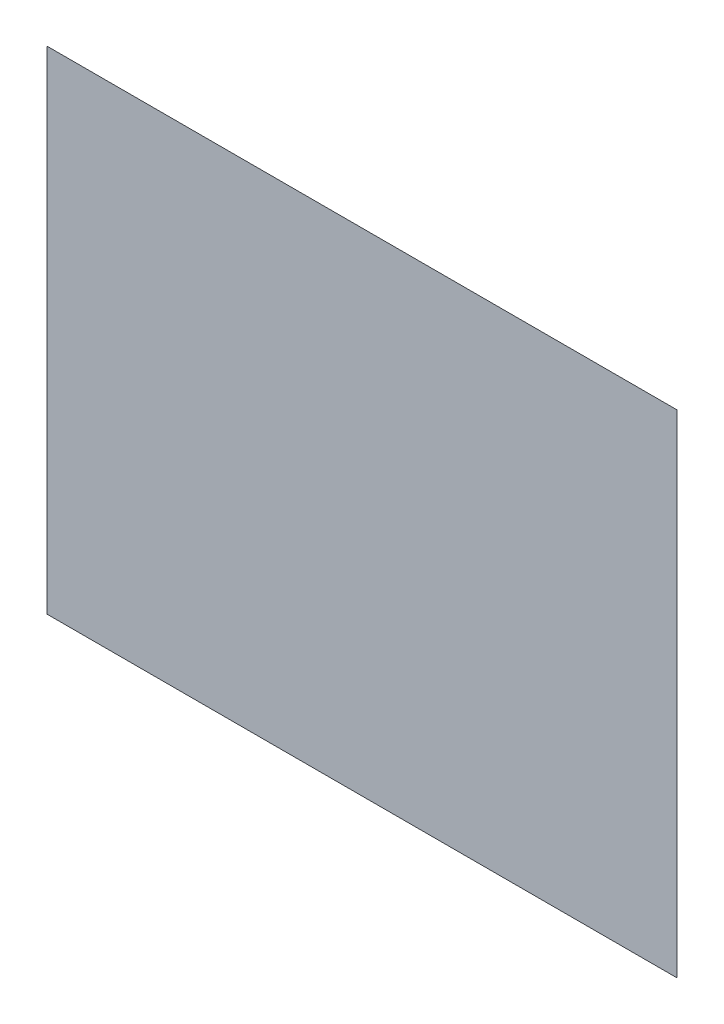
SolidWorks part; units mm, degrees
ref_plane "前视基准面" through (0, 0, 0) normal (0, 0, 1) x (1, 0, 0)
ref_plane "上视基准面" through (0, 0, 0) normal (0, 1, 0) x (1, 0, 0)
ref_plane "右视基准面" through (0, 0, 0) normal (1, 0, 0) x (0, 0, -1)
sketch "草图1" plane through (0, 0, 0) normal (0, 0, 1) x (1, 0, 0)
  line L0 (107.0902, 126.3962) -> (-17.0814, 126.3962) construction
  line L1 (-22.4956, 126.3962) -> (112.5044, 126.3962)
  line L2 (-22.4956, 126.3962) -> (-22.4956, 1.3962)
  line L3 (-22.4956, 1.3962) -> (112.5044, 1.3962)
  line L4 (112.5044, 126.3962) -> (112.5044, 1.3962)
  line L5 (-22.4956, 120.982) -> (-22.4956, 94.3104) construction
  line L6 (112.5044, 94.3104) -> (112.5044, 120.982) construction
  line L7 (-17.0814, 1.3962) -> (107.0902, 1.3962) construction
ref_plane "基准面1" through (0, 0, 100) normal (0, 0, 1) x (1, 0, 0)
sketch "草图2" plane through (0, 0, 100) normal (0, 0, 1) x (1, 0, 0)
  line L0 (-22.4956, 126.3962) -> (112.5044, 126.3962) construction
  line L1 (-122.4956, 226.3962) -> (212.5044, 226.3962)
  line L2 (-122.4956, 226.3962) -> (-122.4956, -35.0038)
  line L3 (-122.4956, -35.0038) -> (212.5044, -35.0038)
  line L4 (212.5044, 226.3962) -> (212.5044, -35.0038)
  line L5 (112.5044, 126.3962) -> (112.5044, 1.3962) construction
  line L6 (-22.4956, 126.3962) -> (-22.4956, 1.3962) construction
  line L7 (-22.4956, 1.3962) -> (112.5044, 1.3962) construction
  dimension "D1" = 100
  dimension "D2" = 100
  dimension "D3" = 100
  dimension "D4" = 36.4
loft "放样1" add profiles "草图2", "草图1"
